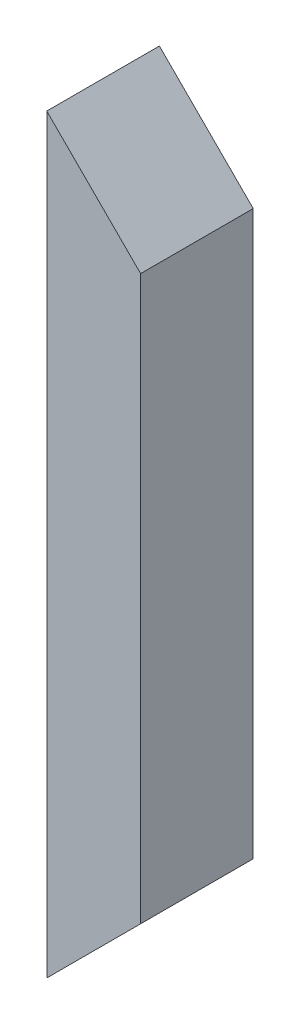
SolidWorks part; units mm, degrees
ref_plane "Front Plane" through (0, 0, 0) normal (0, 0, 1) x (1, 0, 0)
ref_plane "Top Plane" through (0, 0, 0) normal (0, 1, 0) x (1, 0, 0)
ref_plane "Right Plane" through (0, 0, 0) normal (1, 0, 0) x (0, 0, -1)
sketch "Sketch1" plane through (0, 0, 0) normal (0, 1, 0) x (1, 0, 0)
  line L1 (0, 0) -> (25, 0)
  line L2 (0, 0) -> (0, 30)
  line L3 (0, 30) -> (25, 30)
  line L4 (25, 0) -> (25, 30)
  dimension "D1" = 25
  dimension "D2" = 30
extrude "Boss-Extrude1" add sketch "Sketch1" along normal blind 200
sketch "Sketch2" plane through (0, 0, 0) normal (0, 0, 1) x (1, 0, 0)
  line L0 (0, 0) -> (25, 0)
  line L1 (25, 0) -> (25, 25)
  line L2 (25, 200) -> (25, 0) construction
  line L3 (25, 25) -> (0, 0)
  line L4 (25, 175) -> (0, 200)
  line L5 (0, 200) -> (25, 200)
  line L6 (25, 200) -> (25, 175)
  dimension "D1" = 45
  dimension "D2" = 45
extrude "Cut-Extrude1" cut sketch "Sketch2" against normal blind 200
